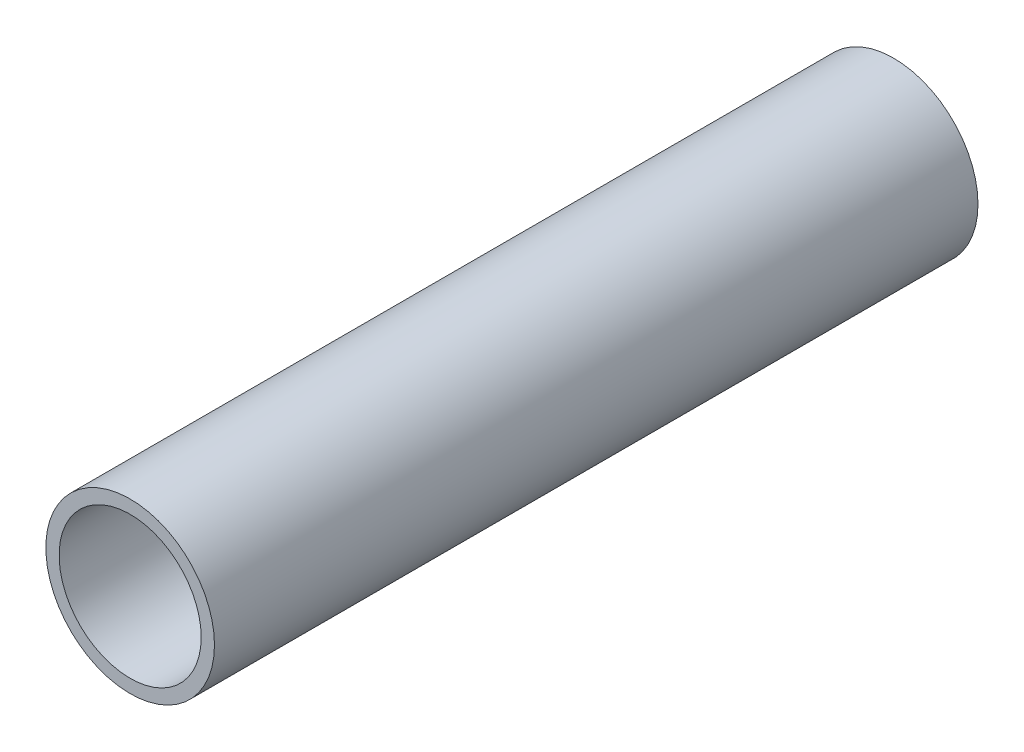
SolidWorks part; units mm, degrees
material "Hexcel AS4C (3000 Filaments)"
ref_plane "Front Plane" through (0, 0, 0) normal (0, 0, 1) x (1, 0, 0)
ref_plane "Top Plane" through (0, 0, 0) normal (0, 1, 0) x (1, 0, 0)
ref_plane "Right Plane" through (0, 0, 0) normal (1, 0, 0) x (0, 0, -1)
sketch "Sketch1" plane through (0, 0, 0) normal (0, 0, 1) x (1, 0, 0)
  circle A0 centre (0, 0) radius 12.7
  circle A1 centre (0, 0) radius 10.7
  dimension "D1" = 25.4
  dimension "D2" = 2
extrude "Boss-Extrude1" add sketch "Sketch1" along normal blind 115
